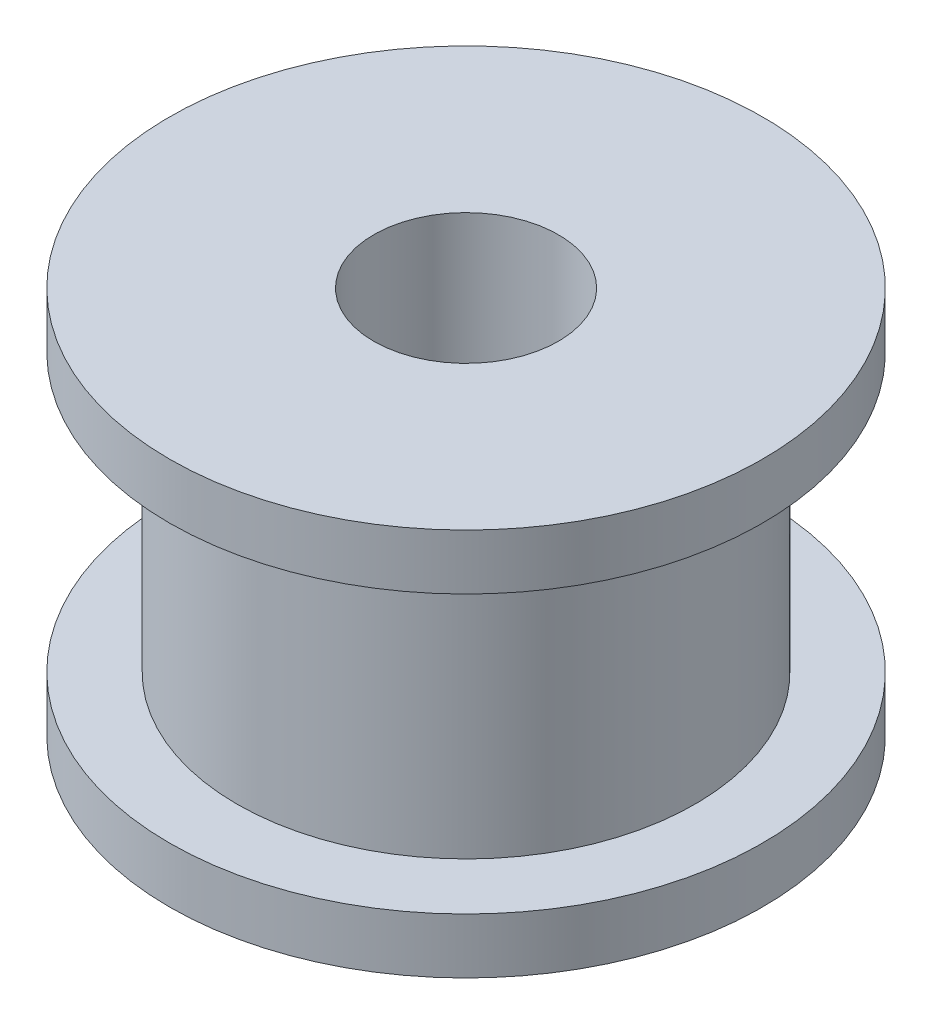
SolidWorks part; units mm, degrees
ref_plane "Front Plane" through (0, 0, 0) normal (0, 0, 1) x (1, 0, 0)
ref_plane "Top Plane" through (0, 0, 0) normal (0, 1, 0) x (1, 0, 0)
ref_plane "Right Plane" through (0, 0, 0) normal (1, 0, 0) x (0, 0, -1)
sketch "Sketch1" plane through (0, 0, 0) normal (0, 1, 0) x (1, 0, 0)
  circle A0 centre (0, 0) radius 8.025
extrude "Boss-Extrude1" add sketch "Sketch1" along normal blind 1.5
sketch "Sketch2" plane through (0, 1.5, 0) normal (0, 1, 0) x (1, 0, 0)
  circle A0 centre (0, 0) radius 6.2
extrude "Boss-Extrude2" add sketch "Sketch2" along normal blind 7.5
sketch "Sketch3" plane through (0, 9, 0) normal (0, 1, 0) x (1, 0, 0)
  circle A0 centre (0, 0) radius 8.025
extrude "Boss-Extrude3" add sketch "Sketch3" along normal blind 1.5
sketch "Sketch4" plane through (0, 10.5, 0) normal (0, 1, 0) x (1, 0, 0)
  circle A0 centre (0, 0) radius 2.5
extrude "Cut-Extrude1" cut sketch "Sketch4" against normal through all
